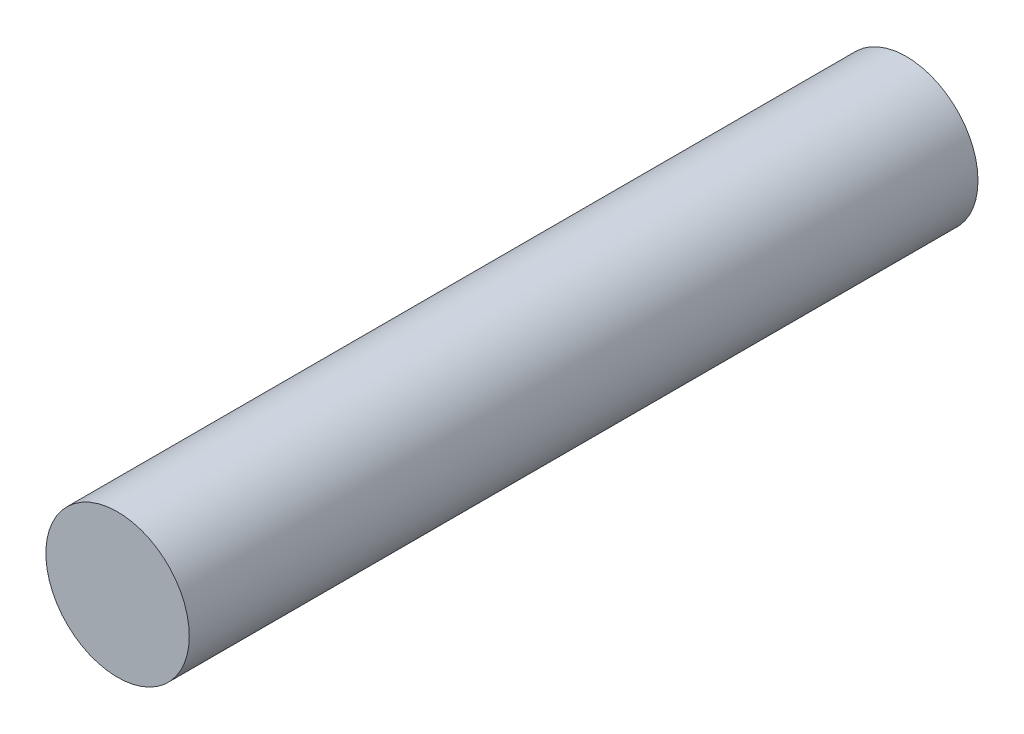
SolidWorks part; units mm, degrees
material "AISI 1020"
ref_plane "Front Plane" through (0, 0, 0) normal (0, 0, 1) x (1, 0, 0)
ref_plane "Top Plane" through (0, 0, 0) normal (0, 1, 0) x (1, 0, 0)
ref_plane "Right Plane" through (0, 0, 0) normal (1, 0, 0) x (0, 0, -1)
sketch "Sketch1" plane through (0, 0, 0) normal (0, 0, 1) x (1, 0, 0)
  circle A0 centre (0, 0) radius 3
extrude "Boss-Extrude1" add sketch "Sketch1" along normal blind 33
